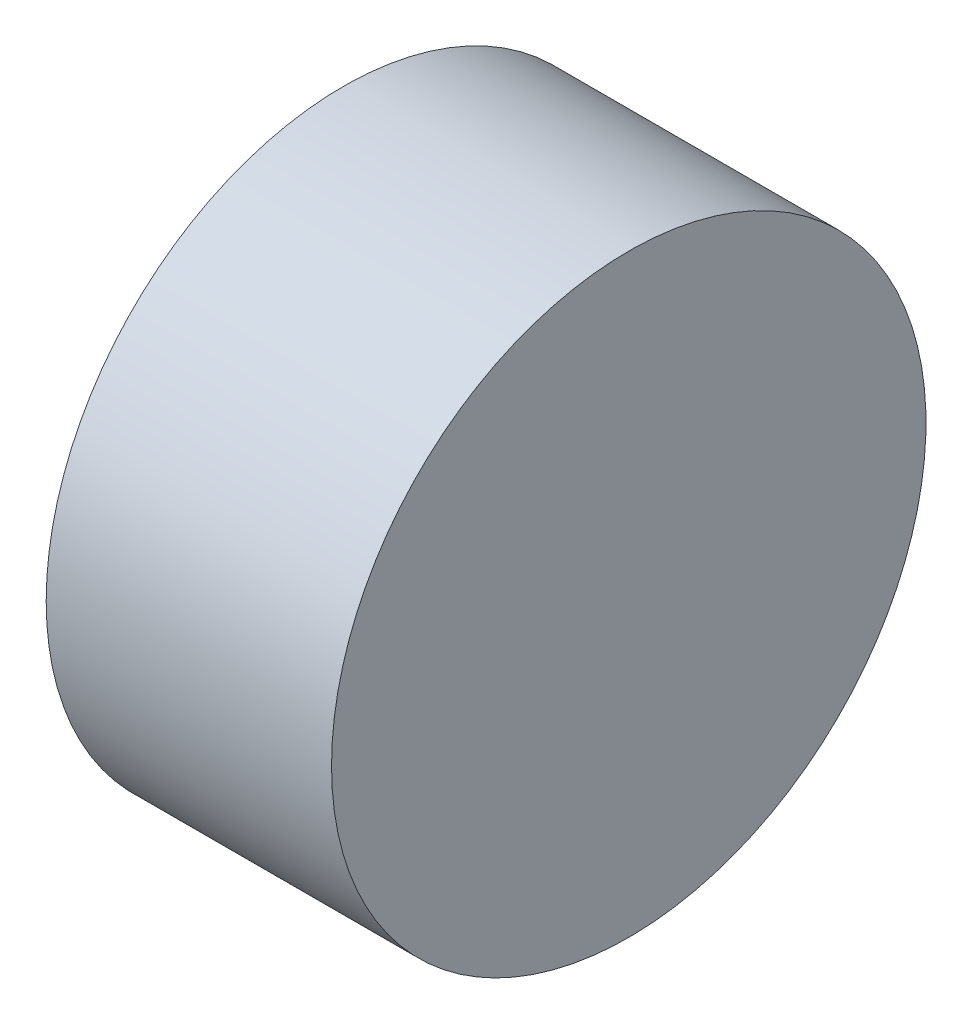
SolidWorks part; units mm, degrees
ref_plane "前视基准面" through (0, 0, 0) normal (0, 0, 1) x (1, 0, 0)
ref_plane "上视基准面" through (0, 0, 0) normal (0, 1, 0) x (1, 0, 0)
ref_plane "右视基准面" through (0, 0, 0) normal (1, 0, 0) x (0, 0, -1)
sketch "草图1" plane through (0, 0, 0) normal (0, 0, 1) x (1, 0, 0)
  line L0 (127.0004, 38.6466) -> (138.8944, 38.6466) construction
  line L1 (130.0786, 38.6466) -> (130.0786, 44.8966)
  line L2 (136.0786, 38.6466) -> (136.0786, 44.8966)
  line L3 (130.0786, 38.6466) -> (136.0786, 38.6466)
  line L5 (130.0786, 44.8966) -> (136.0786, 44.8966)
  dimension "D1" = 6
  dimension "D2" = 6.25
revolve "旋转1" add sketch "草图1" angle 360 about L0
